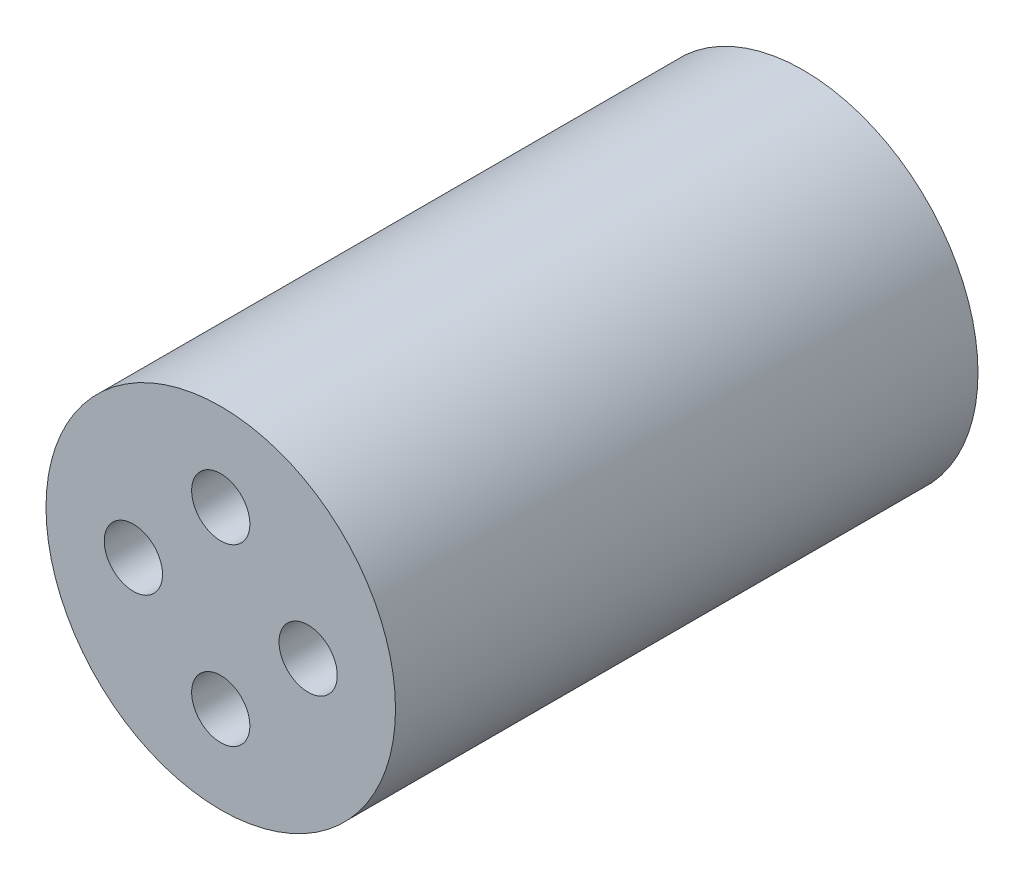
SolidWorks part; units mm, degrees
ref_plane "正面" through (0, 0, 0) normal (0, 0, 1) x (1, 0, 0)
ref_plane "平面" through (0, 0, 0) normal (0, 1, 0) x (1, 0, 0)
ref_plane "右側面" through (0, 0, 0) normal (1, 0, 0) x (0, 0, -1)
sketch "ｽｹｯﾁ1" plane through (0, 0, 0) normal (0, 0, 1) x (1, 0, 0)
  circle A0 centre (0, 0) radius 6
  circle A2 centre (0, 3) radius 1
  circle A3 centre (3, 0) radius 1
  circle A4 centre (0, -3) radius 1
  circle A5 centre (-3, 0) radius 1
  point P15 (0, 0)
  dimension "D1" = 12
  dimension "D3" = 2
  dimension "D4" = 3
  dimension "D5" = 4
extrude "ﾎﾞｽ - 押し出し1" add sketch "ｽｹｯﾁ1" along normal blind 20
